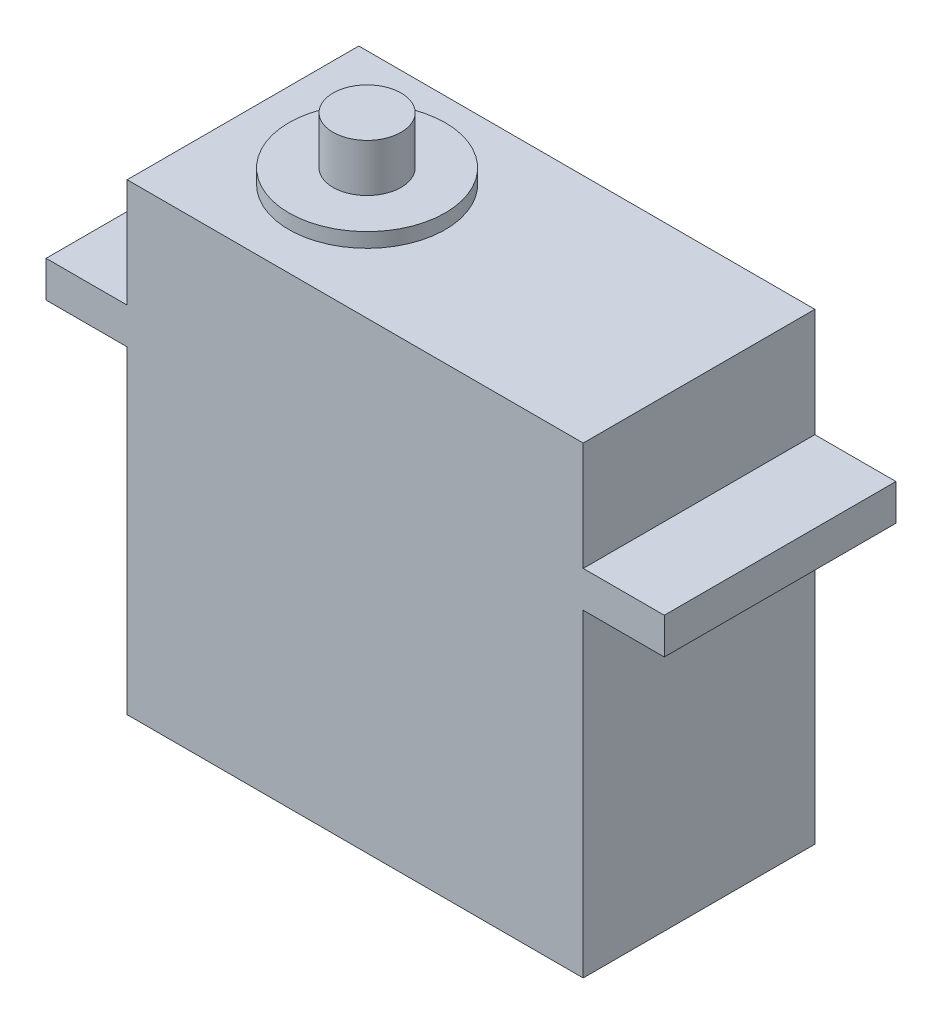
SolidWorks part; units mm, degrees
ref_plane "Front Plane" through (0, 0, 0) normal (0, 0, 1) x (1, 0, 0)
ref_plane "Top Plane" through (0, 0, 0) normal (0, 1, 0) x (1, 0, 0)
ref_plane "Right Plane" through (0, 0, 0) normal (1, 0, 0) x (0, 0, -1)
sketch "Sketch1" plane through (0, 0, 0) normal (0, 0, 1) x (1, 0, 0)
  line L0 (20.0025, 40.64) -> (20.0025, 0) construction
  line L1 (0, 0) -> (40.005, 0)
  line L2 (0, 0) -> (0, 27.94)
  line L3 (0, 40.64) -> (40.005, 40.64)
  line L4 (40.005, 0) -> (40.005, 27.94)
  line L5 (40.005, 31.115) -> (47.117, 31.115)
  line L7 (40.005, 27.94) -> (47.117, 27.94)
  line L8 (47.117, 31.115) -> (47.117, 27.94)
  line L9 (0, 27.94) -> (-7.112, 27.94)
  line L10 (0, 31.115) -> (-7.112, 31.115)
  line L11 (-7.112, 31.115) -> (-7.112, 27.94)
  line L12 (0, 31.115) -> (0, 40.64)
  line L13 (40.005, 31.115) -> (40.005, 40.64)
  dimension "D1" = 40.005
  dimension "D2" = 40.64
  dimension "D3" = 3.175
  dimension "D4" = 7.112
  dimension "D5" = 27.94
extrude "Boss-Extrude1" add sketch "Sketch1" along normal blind 20.32
sketch "Sketch2" plane through (0, 40.64, 0) normal (0, 1, 0) x (1, 0, 0)
  line L0 (0, -10.16) -> (40.005, -10.16) construction
  line L1 (40.005, -20.32) -> (40.005, 0) construction
  line L4 (40.005, 0) -> (0, 0)
  line L5 (0, 0) -> (0, -20.32)
  line L6 (0, -20.32) -> (40.005, -20.32)
  line L7 (40.005, -20.32) -> (40.005, 0)
  line L8 (40.005, 0) -> (0, 0) construction
  line L9 (0, 0) -> (0, -20.32) construction
  line L10 (0, -20.32) -> (40.005, -20.32) construction
  line L11 (40.005, -20.32) -> (40.005, 0) construction
  circle A0 centre (10.8863, -10.16) radius 6.858
  point P8 (40.005, -10.16)
  point P11 (0, 0)
  dimension "D2" = 13.716
  dimension "D1" = 0
extrude "Boss-Extrude2" add sketch "Sketch2" along normal blind 1.27
sketch "Sketch3" plane through (0, 41.91, 0) normal (0, 1, 0) x (1, 0, 0)
  circle A0 centre (10.8863, -10.16) radius 2.9845
  circle A1 centre (10.8863, -10.16) radius 6.858
  circle A2 centre (10.8863, -10.16) radius 6.858 construction
  dimension "D2" = 5.969
  dimension "D1" = 0
extrude "Boss-Extrude3" add sketch "Sketch3" along normal blind 4.191
